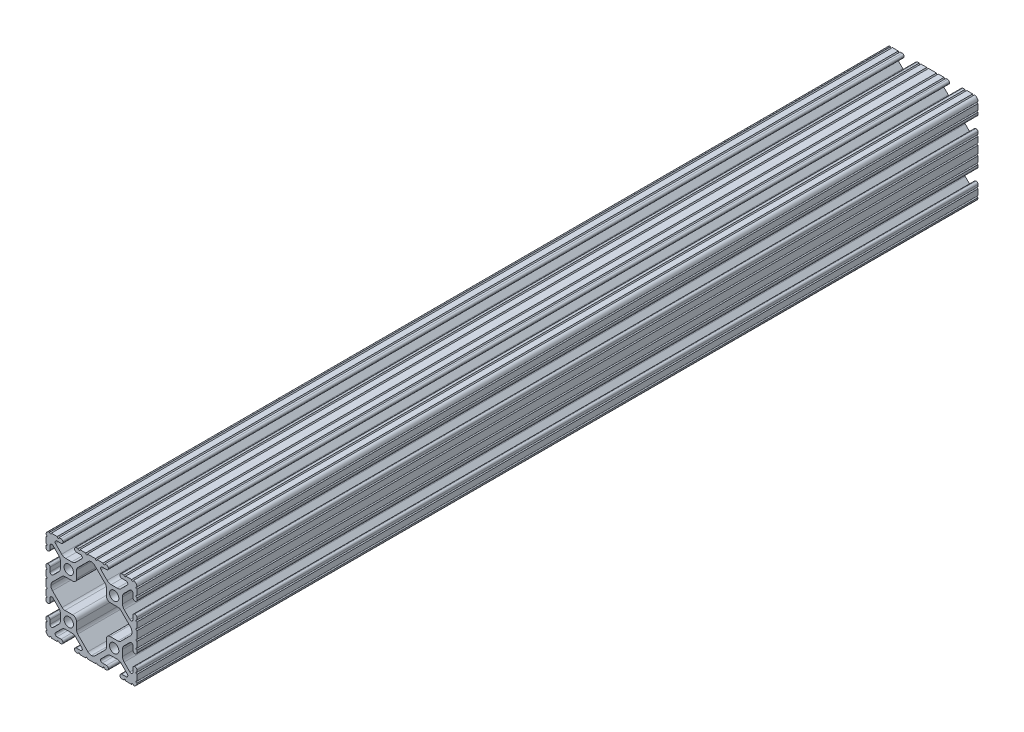
SolidWorks part; units mm, degrees
material "6105-T5 Aluminum"
ref_plane "Front Plane" through (0, 0, 0) normal (0, 0, 1) x (1, 0, 0)
ref_plane "Top Plane" through (0, 0, 0) normal (0, 1, 0) x (1, 0, 0)
ref_plane "Right Plane" through (0, 0, 0) normal (1, 0, 0) x (0, 0, -1)
sketch "Sketch1" plane through (0, 0, 0) normal (0, 0, 1) x (1, 0, 0)
  line L0 (-7.684, -16.0797) -> (-1.9878, -21.7759)
  line L1 (-8.3312, -10.3886) -> (-8.3312, -14.5171)
  line L2 (-14.8165, -8.1788) -> (-10.541, -8.1788)
  line L3 (-21.7734, -2.1502) -> (-16.3772, -7.5334)
  line L4 (-22.6314, 0.0822) -> (-22.6314, -0.0822)
  line L5 (-16.3772, 7.5334) -> (-21.7734, 2.1502)
  line L6 (-10.541, 8.1788) -> (-14.8165, 8.1788)
  line L7 (-8.3312, 14.5171) -> (-8.3312, 10.3886)
  line L8 (-1.7956, 21.9681) -> (-7.684, 16.0797)
  line L9 (7.684, 16.0797) -> (1.7956, 21.9681)
  line L10 (8.3312, 10.389) -> (8.3312, 14.5171)
  line L11 (14.8161, 8.1792) -> (10.541, 8.1792)
  line L12 (21.7734, 2.1502) -> (16.3768, 7.5339)
  line L13 (22.6314, -0.0822) -> (22.6314, 0.0822)
  line L14 (16.3772, -7.5334) -> (21.7734, -2.1502)
  line L15 (10.541, -8.1788) -> (14.8165, -8.1788)
  line L16 (8.3312, -14.5171) -> (8.3312, -10.3886)
  line L17 (1.9878, -21.7759) -> (7.684, -16.0797)
  line L18 (7.4579, -25.3998) -> (8.4051, -25.3998)
  line L19 (9.4615, -24.3585) -> (9.4615, -24.2315)
  line L20 (8.4051, -23.1902) -> (6.0878, -23.1902)
  line L21 (5.388, -21.5008) -> (8.763, -18.1257)
  line L22 (11.0081, -17.1958) -> (14.3919, -17.1958)
  line L23 (16.637, -18.1257) -> (20.012, -21.5008)
  line L24 (19.2977, -23.1901) -> (16.9799, -23.1901)
  line L25 (15.9385, -24.2315) -> (15.9385, -24.3585)
  line L26 (16.9949, -25.3998) -> (18.134, -25.3998)
  line L27 (19.1384, -25.3998) -> (22.4132, -25.3998)
  line L28 (23.4176, -25.3998) -> (23.4501, -25.3998)
  line L29 (25.4, -23.2975) -> (25.4, -23.2686)
  line L30 (25.4, -22.2526) -> (25.4, -19.0252)
  line L31 (25.4, -18.0092) -> (25.4, -16.916)
  line L32 (24.3586, -15.8746) -> (24.2316, -15.8746)
  line L33 (23.1902, -16.916) -> (23.1902, -19.101)
  line L34 (21.4558, -19.8194) -> (18.2781, -16.6418)
  line L35 (17.3482, -14.3967) -> (17.3482, -11.0035)
  line L36 (18.2808, -8.7557) -> (21.4566, -5.5875)
  line L37 (23.1902, -6.3068) -> (23.1902, -8.484)
  line L38 (24.2316, -9.5254) -> (24.3586, -9.5254)
  line L39 (25.4, -8.484) -> (25.4, -7.3277)
  line L40 (25.4, -6.3117) -> (25.4, -3.0843)
  line L41 (25.4, -2.0683) -> (25.4, 2.0683)
  line L42 (25.4, 3.0843) -> (25.4, 6.3117)
  line L43 (25.4, 7.3277) -> (25.4, 8.484)
  line L44 (24.3586, 9.5254) -> (24.2316, 9.5254)
  line L45 (23.1902, 8.484) -> (23.1902, 6.3068)
  line L46 (21.4566, 5.5875) -> (18.2808, 8.7557)
  line L47 (17.3482, 11.0035) -> (17.3482, 14.3967)
  line L48 (18.2781, 16.6418) -> (21.4558, 19.8194)
  line L49 (23.1902, 19.101) -> (23.1902, 16.916)
  line L50 (24.2316, 15.8746) -> (24.3586, 15.8746)
  line L51 (25.4, 16.916) -> (25.4, 18.0092)
  line L52 (25.4, 19.0252) -> (25.4, 22.2526)
  line L53 (25.4, 23.2686) -> (25.4, 23.2975)
  line L54 (23.4501, 25.3998) -> (23.4176, 25.3998)
  line L55 (22.4132, 25.3998) -> (19.1384, 25.3998)
  line L56 (18.134, 25.3998) -> (16.9949, 25.3998)
  line L57 (15.9385, 24.3585) -> (15.9385, 24.2315)
  line L58 (16.9799, 23.1901) -> (19.2977, 23.1901)
  line L59 (20.012, 21.5008) -> (16.637, 18.1257)
  line L60 (14.3919, 17.1958) -> (11.0081, 17.1958)
  line L61 (8.763, 18.1257) -> (5.388, 21.5008)
  line L62 (6.0878, 23.1902) -> (8.4051, 23.1902)
  line L63 (9.4615, 24.2315) -> (9.4615, 24.3585)
  line L64 (8.4051, 25.3998) -> (7.4579, 25.3998)
  line L65 (6.4535, 25.3998) -> (3.2145, 25.3998)
  line L66 (2.2101, 25.3998) -> (-2.2101, 25.3998)
  line L67 (-3.2145, 25.3998) -> (-6.4535, 25.3998)
  line L68 (-7.4579, 25.3998) -> (-8.4051, 25.3998)
  line L69 (-9.4615, 24.3585) -> (-9.4615, 24.2315)
  line L70 (-8.4051, 23.1902) -> (-6.0878, 23.1902)
  line L71 (-5.388, 21.5008) -> (-8.763, 18.1257)
  line L72 (-11.0081, 17.1958) -> (-14.3919, 17.1958)
  line L73 (-16.637, 18.1257) -> (-20.012, 21.5008)
  line L74 (-19.2977, 23.1901) -> (-16.9799, 23.1901)
  line L75 (-15.9385, 24.2315) -> (-15.9385, 24.3585)
  line L76 (-16.9949, 25.3998) -> (-18.134, 25.3998)
  line L77 (-19.1384, 25.3998) -> (-22.4132, 25.3998)
  line L78 (-23.4176, 25.3998) -> (-23.4501, 25.3998)
  line L79 (-25.4, 23.2975) -> (-25.4, 23.2686)
  line L80 (-25.4, 22.2526) -> (-25.4, 19.0252)
  line L81 (-25.4, 18.0092) -> (-25.4, 16.916)
  line L82 (-24.3586, 15.8746) -> (-24.2316, 15.8746)
  line L83 (-23.1902, 16.916) -> (-23.1902, 19.101)
  line L84 (-21.4558, 19.8194) -> (-18.2781, 16.6418)
  line L85 (-17.3482, 14.3967) -> (-17.3482, 11.0035)
  line L86 (-18.2808, 8.7557) -> (-21.4566, 5.5875)
  line L87 (-23.1902, 6.3068) -> (-23.1902, 8.484)
  line L88 (-24.2316, 9.5254) -> (-24.3586, 9.5254)
  line L89 (-25.4, 8.484) -> (-25.4, 7.3277)
  line L90 (-25.4, 6.3117) -> (-25.4, 3.0843)
  line L91 (-25.4, 2.0683) -> (-25.4, -2.0683)
  line L92 (-25.4, -3.0843) -> (-25.4, -6.3117)
  line L93 (-25.4, -7.3277) -> (-25.4, -8.484)
  line L94 (-24.3586, -9.5254) -> (-24.2316, -9.5254)
  line L95 (-23.1902, -8.484) -> (-23.1902, -6.3068)
  line L96 (-21.4566, -5.5875) -> (-18.2808, -8.7557)
  line L97 (-17.3482, -11.0035) -> (-17.3482, -14.3967)
  line L98 (-18.2781, -16.6418) -> (-21.4558, -19.8194)
  line L99 (-23.1902, -19.101) -> (-23.1902, -16.916)
  line L100 (-24.2316, -15.8746) -> (-24.3586, -15.8746)
  line L101 (-25.4, -16.916) -> (-25.4, -18.0092)
  line L102 (-25.4, -19.0252) -> (-25.4, -22.2526)
  line L103 (-25.4, -23.2686) -> (-25.4, -23.2975)
  line L104 (-23.4501, -25.3998) -> (-23.4176, -25.3998)
  line L105 (-22.4132, -25.3998) -> (-19.1384, -25.3998)
  line L106 (-18.134, -25.3998) -> (-16.9949, -25.3998)
  line L107 (-15.9385, -24.3585) -> (-15.9385, -24.2315)
  line L108 (-16.9799, -23.1901) -> (-19.2977, -23.1901)
  line L109 (-20.012, -21.5008) -> (-16.637, -18.1257)
  line L110 (-14.3919, -17.1958) -> (-11.0081, -17.1958)
  line L111 (-8.763, -18.1257) -> (-5.388, -21.5008)
  line L112 (-6.0878, -23.1902) -> (-8.4051, -23.1902)
  line L113 (-9.4615, -24.2315) -> (-9.4615, -24.3585)
  line L114 (-8.4051, -25.3998) -> (-7.4579, -25.3998)
  line L115 (-6.4535, -25.3998) -> (-3.2145, -25.3998)
  line L116 (-2.2101, -25.3998) -> (2.2101, -25.3998)
  line L117 (3.2145, -25.3998) -> (6.4535, -25.3998)
  circle A0 centre (12.7, 12.7) radius 2.6035
  circle A1 centre (-12.7, 12.7) radius 2.6035
  circle A2 centre (-12.7, -12.7) radius 2.6035
  arc A3 (0, -22.6304) -> (1.9878, -21.7759) centre (-0.0777, -19.7104) ccw
  arc A4 (-1.9878, -21.7759) -> (0, -22.6304) centre (0.0777, -19.7104) ccw
  arc A5 (-8.3312, -14.5171) -> (-7.684, -16.0797) centre (-6.1214, -14.5171) ccw
  arc A6 (-8.3312, -10.3886) -> (-10.541, -8.1788) centre (-10.541, -10.3886) ccw
  arc A7 (-16.3772, -7.5334) -> (-14.8165, -8.1788) centre (-14.8165, -5.969) ccw
  arc A8 (-22.6314, -0.0822) -> (-21.7734, -2.1502) centre (-19.7104, -0.0822) ccw
  arc A9 (-21.7734, 2.1502) -> (-22.6314, 0.0822) centre (-19.7104, 0.0822) ccw
  arc A10 (-14.8165, 8.1788) -> (-16.3772, 7.5334) centre (-14.8165, 5.969) ccw
  arc A11 (-10.541, 8.1788) -> (-8.3312, 10.3886) centre (-10.541, 10.3886) ccw
  arc A12 (-7.684, 16.0797) -> (-8.3312, 14.5171) centre (-6.1214, 14.5171) ccw
  arc A13 (0, 22.8111) -> (-1.7956, 21.9681) centre (0.2699, 19.9026) ccw
  arc A14 (1.7956, 21.9681) -> (0, 22.8111) centre (-0.2699, 19.9026) ccw
  arc A15 (8.3312, 14.5171) -> (7.684, 16.0797) centre (6.1214, 14.5171) ccw
  arc A16 (8.3312, 10.389) -> (10.541, 8.1792) centre (10.541, 10.389) ccw
  arc A17 (16.3768, 7.5339) -> (14.8161, 8.1792) centre (14.8161, 5.9694) ccw
  arc A18 (22.6314, 0.0822) -> (21.7734, 2.1502) centre (19.7104, 0.0822) ccw
  arc A19 (21.7734, -2.1502) -> (22.6314, -0.0822) centre (19.7104, -0.0822) ccw
  arc A20 (14.8165, -8.1788) -> (16.3772, -7.5334) centre (14.8165, -5.969) ccw
  arc A21 (10.541, -8.1788) -> (8.3312, -10.3886) centre (10.541, -10.3886) ccw
  arc A22 (7.684, -16.0797) -> (8.3312, -14.5171) centre (6.1214, -14.5171) ccw
  circle A23 centre (12.7, -12.7) radius 2.6035
  arc A24 (7.4579, -25.3998) -> (6.4535, -25.3998) centre (6.9557, -25.3232) ccw
  arc A25 (8.4051, -25.3998) -> (9.4615, -24.3585) centre (8.4201, -24.3585) ccw
  arc A26 (9.4615, -24.2315) -> (8.4051, -23.1902) centre (8.4201, -24.2315) ccw
  arc A27 (5.388, -21.5008) -> (6.0878, -23.1902) centre (6.0878, -22.2006) ccw
  arc A28 (11.0081, -17.1958) -> (8.763, -18.1257) centre (11.0081, -20.3708) ccw
  arc A29 (16.637, -18.1257) -> (14.3919, -17.1958) centre (14.3919, -20.3708) ccw
  arc A30 (19.2977, -23.1901) -> (20.012, -21.5008) centre (19.3122, -22.2006) ccw
  arc A31 (16.9799, -23.1901) -> (15.9385, -24.2315) centre (16.9799, -24.2315) ccw
  arc A32 (15.9385, -24.3585) -> (16.9949, -25.3998) centre (16.9799, -24.3585) ccw
  arc A33 (19.1384, -25.3998) -> (18.134, -25.3998) centre (18.6362, -25.3232) ccw
  arc A34 (23.4176, -25.3998) -> (22.4132, -25.3998) centre (22.9154, -25.3232) ccw
  arc A35 (23.4501, -25.3998) -> (25.4, -23.2975) centre (23.2918, -23.2975) ccw
  arc A36 (25.4, -22.2526) -> (25.4, -23.2686) centre (25.4, -22.7606) ccw
  arc A37 (25.4, -18.0092) -> (25.4, -19.0252) centre (25.4, -18.5172) ccw
  arc A38 (25.4, -16.916) -> (24.3586, -15.8746) centre (24.3586, -16.916) ccw
  arc A39 (24.2316, -15.8746) -> (23.1902, -16.916) centre (24.2316, -16.916) ccw
  arc A40 (21.4558, -19.8194) -> (23.1902, -19.101) centre (22.1742, -19.101) ccw
  arc A41 (17.3482, -14.3967) -> (18.2781, -16.6418) centre (20.5232, -14.3967) ccw
  arc A42 (18.2808, -8.7557) -> (17.3482, -11.0035) centre (20.5232, -11.0035) ccw
  arc A43 (23.1902, -6.3068) -> (21.4566, -5.5875) centre (22.1742, -6.3068) ccw
  arc A44 (23.1902, -8.484) -> (24.2316, -9.5254) centre (24.2316, -8.484) ccw
  arc A45 (24.3586, -9.5254) -> (25.4, -8.484) centre (24.3586, -8.484) ccw
  arc A46 (25.4, -6.3117) -> (25.4, -7.3277) centre (25.4, -6.8197) ccw
  arc A47 (25.4, -2.0683) -> (25.4, -3.0843) centre (25.4, -2.5763) ccw
  arc A48 (25.4, 3.0843) -> (25.4, 2.0683) centre (25.4, 2.5763) ccw
  arc A49 (25.4, 7.3277) -> (25.4, 6.3117) centre (25.4, 6.8197) ccw
  arc A50 (25.4, 8.484) -> (24.3586, 9.5254) centre (24.3586, 8.484) ccw
  arc A51 (24.2316, 9.5254) -> (23.1902, 8.484) centre (24.2316, 8.484) ccw
  arc A52 (21.4566, 5.5875) -> (23.1902, 6.3068) centre (22.1742, 6.3068) ccw
  arc A53 (17.3482, 11.0035) -> (18.2808, 8.7557) centre (20.5232, 11.0035) ccw
  arc A54 (18.2781, 16.6418) -> (17.3482, 14.3967) centre (20.5232, 14.3967) ccw
  arc A55 (23.1902, 19.101) -> (21.4558, 19.8194) centre (22.1742, 19.101) ccw
  arc A56 (23.1902, 16.916) -> (24.2316, 15.8746) centre (24.2316, 16.916) ccw
  arc A57 (24.3586, 15.8746) -> (25.4, 16.916) centre (24.3586, 16.916) ccw
  arc A58 (25.4, 19.0252) -> (25.4, 18.0092) centre (25.4, 18.5172) ccw
  arc A59 (25.4, 23.2686) -> (25.4, 22.2526) centre (25.4, 22.7606) ccw
  arc A60 (25.4, 23.2975) -> (23.4501, 25.3998) centre (23.2918, 23.2975) ccw
  arc A61 (22.4132, 25.3998) -> (23.4176, 25.3998) centre (22.9154, 25.3232) ccw
  arc A62 (18.134, 25.3998) -> (19.1384, 25.3998) centre (18.6362, 25.3232) ccw
  arc A63 (16.9949, 25.3998) -> (15.9385, 24.3585) centre (16.9799, 24.3585) ccw
  arc A64 (15.9385, 24.2315) -> (16.9799, 23.1901) centre (16.9799, 24.2315) ccw
  arc A65 (20.012, 21.5008) -> (19.2977, 23.1901) centre (19.3122, 22.2006) ccw
  arc A66 (14.3919, 17.1958) -> (16.637, 18.1257) centre (14.3919, 20.3708) ccw
  arc A67 (8.763, 18.1257) -> (11.0081, 17.1958) centre (11.0081, 20.3708) ccw
  arc A68 (6.0878, 23.1902) -> (5.388, 21.5008) centre (6.0878, 22.2006) ccw
  arc A69 (8.4051, 23.1902) -> (9.4615, 24.2315) centre (8.4201, 24.2315) ccw
  arc A70 (9.4615, 24.3585) -> (8.4051, 25.3998) centre (8.4201, 24.3585) ccw
  arc A71 (6.4535, 25.3998) -> (7.4579, 25.3998) centre (6.9557, 25.3232) ccw
  arc A72 (2.2101, 25.3998) -> (3.2145, 25.3998) centre (2.7123, 25.3232) ccw
  arc A73 (-3.2145, 25.3998) -> (-2.2101, 25.3998) centre (-2.7123, 25.3232) ccw
  arc A74 (-7.4579, 25.3998) -> (-6.4535, 25.3998) centre (-6.9557, 25.3232) ccw
  arc A75 (-8.4051, 25.3998) -> (-9.4615, 24.3585) centre (-8.4201, 24.3585) ccw
  arc A76 (-9.4615, 24.2315) -> (-8.4051, 23.1902) centre (-8.4201, 24.2315) ccw
  arc A77 (-5.388, 21.5008) -> (-6.0878, 23.1902) centre (-6.0878, 22.2006) ccw
  arc A78 (-11.0081, 17.1958) -> (-8.763, 18.1257) centre (-11.0081, 20.3708) ccw
  arc A79 (-16.637, 18.1257) -> (-14.3919, 17.1958) centre (-14.3919, 20.3708) ccw
  arc A80 (-19.2977, 23.1901) -> (-20.012, 21.5008) centre (-19.3122, 22.2006) ccw
  arc A81 (-16.9799, 23.1901) -> (-15.9385, 24.2315) centre (-16.9799, 24.2315) ccw
  arc A82 (-15.9385, 24.3585) -> (-16.9949, 25.3998) centre (-16.9799, 24.3585) ccw
  arc A83 (-19.1384, 25.3998) -> (-18.134, 25.3998) centre (-18.6362, 25.3232) ccw
  arc A84 (-23.4176, 25.3998) -> (-22.4132, 25.3998) centre (-22.9154, 25.3232) ccw
  arc A85 (-23.4501, 25.3998) -> (-25.4, 23.2975) centre (-23.2918, 23.2975) ccw
  arc A86 (-25.4, 22.2526) -> (-25.4, 23.2686) centre (-25.4, 22.7606) ccw
  arc A87 (-25.4, 18.0092) -> (-25.4, 19.0252) centre (-25.4, 18.5172) ccw
  arc A88 (-25.4, 16.916) -> (-24.3586, 15.8746) centre (-24.3586, 16.916) ccw
  arc A89 (-24.2316, 15.8746) -> (-23.1902, 16.916) centre (-24.2316, 16.916) ccw
  arc A90 (-21.4558, 19.8194) -> (-23.1902, 19.101) centre (-22.1742, 19.101) ccw
  arc A91 (-17.3482, 14.3967) -> (-18.2781, 16.6418) centre (-20.5232, 14.3967) ccw
  arc A92 (-18.2808, 8.7557) -> (-17.3482, 11.0035) centre (-20.5232, 11.0035) ccw
  arc A93 (-23.1902, 6.3068) -> (-21.4566, 5.5875) centre (-22.1742, 6.3068) ccw
  arc A94 (-23.1902, 8.484) -> (-24.2316, 9.5254) centre (-24.2316, 8.484) ccw
  arc A95 (-24.3586, 9.5254) -> (-25.4, 8.484) centre (-24.3586, 8.484) ccw
  arc A96 (-25.4, 6.3117) -> (-25.4, 7.3277) centre (-25.4, 6.8197) ccw
  arc A97 (-25.4, 2.0683) -> (-25.4, 3.0843) centre (-25.4, 2.5763) ccw
  arc A98 (-25.4, -3.0843) -> (-25.4, -2.0683) centre (-25.4, -2.5763) ccw
  arc A99 (-25.4, -7.3277) -> (-25.4, -6.3117) centre (-25.4, -6.8197) ccw
  arc A100 (-25.4, -8.484) -> (-24.3586, -9.5254) centre (-24.3586, -8.484) ccw
  arc A101 (-24.2316, -9.5254) -> (-23.1902, -8.484) centre (-24.2316, -8.484) ccw
  arc A102 (-21.4566, -5.5875) -> (-23.1902, -6.3068) centre (-22.1742, -6.3068) ccw
  arc A103 (-17.3482, -11.0035) -> (-18.2808, -8.7557) centre (-20.5232, -11.0035) ccw
  arc A104 (-18.2781, -16.6418) -> (-17.3482, -14.3967) centre (-20.5232, -14.3967) ccw
  arc A105 (-23.1902, -19.101) -> (-21.4558, -19.8194) centre (-22.1742, -19.101) ccw
  arc A106 (-23.1902, -16.916) -> (-24.2316, -15.8746) centre (-24.2316, -16.916) ccw
  arc A107 (-24.3586, -15.8746) -> (-25.4, -16.916) centre (-24.3586, -16.916) ccw
  arc A108 (-25.4, -19.0252) -> (-25.4, -18.0092) centre (-25.4, -18.5172) ccw
  arc A109 (-25.4, -23.2686) -> (-25.4, -22.2526) centre (-25.4, -22.7606) ccw
  arc A110 (-25.4, -23.2975) -> (-23.4501, -25.3998) centre (-23.2918, -23.2975) ccw
  arc A111 (-22.4132, -25.3998) -> (-23.4176, -25.3998) centre (-22.9154, -25.3232) ccw
  arc A112 (-18.134, -25.3998) -> (-19.1384, -25.3998) centre (-18.6362, -25.3232) ccw
  arc A113 (-16.9949, -25.3998) -> (-15.9385, -24.3585) centre (-16.9799, -24.3585) ccw
  arc A114 (-15.9385, -24.2315) -> (-16.9799, -23.1901) centre (-16.9799, -24.2315) ccw
  arc A115 (-20.012, -21.5008) -> (-19.2977, -23.1901) centre (-19.3122, -22.2006) ccw
  arc A116 (-14.3919, -17.1958) -> (-16.637, -18.1257) centre (-14.3919, -20.3708) ccw
  arc A117 (-8.763, -18.1257) -> (-11.0081, -17.1958) centre (-11.0081, -20.3708) ccw
  arc A118 (-6.0878, -23.1902) -> (-5.388, -21.5008) centre (-6.0878, -22.2006) ccw
  arc A119 (-8.4051, -23.1902) -> (-9.4615, -24.2315) centre (-8.4201, -24.2315) ccw
  arc A120 (-9.4615, -24.3585) -> (-8.4051, -25.3998) centre (-8.4201, -24.3585) ccw
  arc A121 (-6.4535, -25.3998) -> (-7.4579, -25.3998) centre (-6.9557, -25.3232) ccw
  arc A122 (-2.2101, -25.3998) -> (-3.2145, -25.3998) centre (-2.7123, -25.3232) ccw
  arc A123 (3.2145, -25.3998) -> (2.2101, -25.3998) centre (2.7123, -25.3232) ccw
extrude "Extrude1" add sketch "Sketch1" against normal mid plane 470
